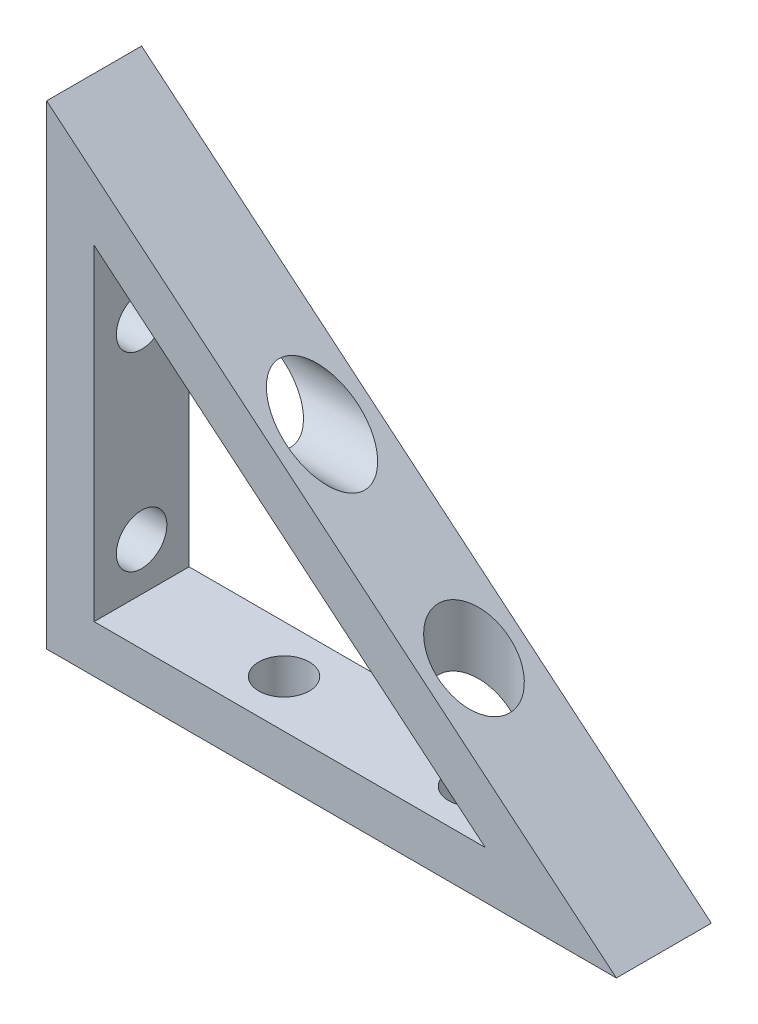
SolidWorks part; units mm, degrees
ref_plane "Front Plane" through (0, 0, 0) normal (0, 0, 1) x (1, 0, 0)
ref_plane "Top Plane" through (0, 0, 0) normal (0, 1, 0) x (1, 0, 0)
ref_plane "Right Plane" through (0, 0, 0) normal (1, 0, 0) x (0, 0, -1)
sketch "Sketch1" plane through (0, 0, 0) normal (0, 0, 1) x (1, 0, 0)
  line L0 (0, 0) -> (0, 63.5)
  line L1 (0, 63.5) -> (76.2, 0)
  line L2 (76.2, 0) -> (0, 0)
  line L3 (6.35, 49.9425) -> (6.35, 6.35)
  line L4 (6.35, 6.35) -> (58.661, 6.35)
  line L5 (58.661, 6.35) -> (6.35, 49.9425)
  dimension "D1" = 6.35
  dimension "D2" = 6.35
  dimension "D3" = 6.35
  dimension "D4" = 63.5
  dimension "D5" = 76.2
extrude "Boss-Extrude1" add sketch "Sketch1" along normal blind 12.7
hole_wizard "1/4 Clearance Hole1" positions "Sketch3" profile "Sketch2" hole size "1/4" standard "ANSI Inch"
sketch "Sketch3" plane through (6.35, 0, 0) normal (1, 0, 0) x (0, 0, -1)
  line L0 (-12.7, 0) -> (0, 0) construction
  line L1 (-12.7, 63.5) -> (-12.7, 0) construction
  point P0 (-6.35, 12.7)
  point P2 (-6.35, 38.1)
  dimension "D1" = 12.7
  dimension "D2" = 25.4
  dimension "D3" = 6.35
sketch "Sketch2" plane through (6.35, 12.7, 6.35) normal (0, 1, 0) x (0, 0, -1)
  line L0 (0, 0) -> (0, 6.35)
  line L1 (0, 6.35) -> (3.3782, 6.35)
  line L2 (3.3782, 6.35) -> (3.3782, 0)
  line L5 (3.3782, 0) -> (0, 0)
  line L11 (0, -6.35) -> (0, 107.95) construction
  dimension "Thru Hole Dia." = 6.7564
  dimension "Thru Hole Depth" = 6.35
hole_wizard "1/4 Clearance Hole2" positions "Sketch5" profile "Sketch4" hole size "1/4" standard "ANSI Inch"
sketch "Sketch5" plane through (0, 6.35, 0) normal (0, 1, 0) x (1, 0, 0)
  line L0 (0, -12.7) -> (0, 0) construction
  line L1 (0, 0) -> (76.2, 0) construction
  point P0 (25.4, -6.35)
  point P2 (50.8, -6.35)
  point P5 (0, -6.35)
  dimension "D1" = 25.4
  dimension "D2" = 25.4
  dimension "D3" = 6.35
sketch "Sketch4" plane through (25.4, 6.35, 6.35) normal (1, 0, 0) x (0, 0, 1)
  line L0 (0, 0) -> (0, 6.35)
  line L1 (0, 6.35) -> (3.3782, 6.35)
  line L2 (3.3782, 6.35) -> (3.3782, 0)
  line L5 (3.3782, 0) -> (0, 0)
  line L11 (0, -6.35) -> (0, 107.95) construction
  dimension "Thru Hole Dia." = 6.7564
  dimension "Thru Hole Depth" = 6.35
sketch "Sketch6" plane through (6.35, 0, 0) normal (1, 0, 0) x (0, 0, -1)
  circle A0 centre (-6.35, 38.1) radius 4.7625
  dimension "D1" = 9.525
extrude "Cut-Extrude1" cut sketch "Sketch6" along normal through all
sketch "Sketch7" plane through (0, 6.35, 0) normal (0, 1, 0) x (1, 0, 0)
  circle A0 centre (50.8, -6.35) radius 4.7625
  dimension "D1" = 9.525
extrude "Cut-Extrude2" cut sketch "Sketch7" along normal through all
equation "\"D2@Sketch1\"=\"D1@Sketch1\""
equation "\"D3@Sketch1\"=\"D1@Sketch1\""
